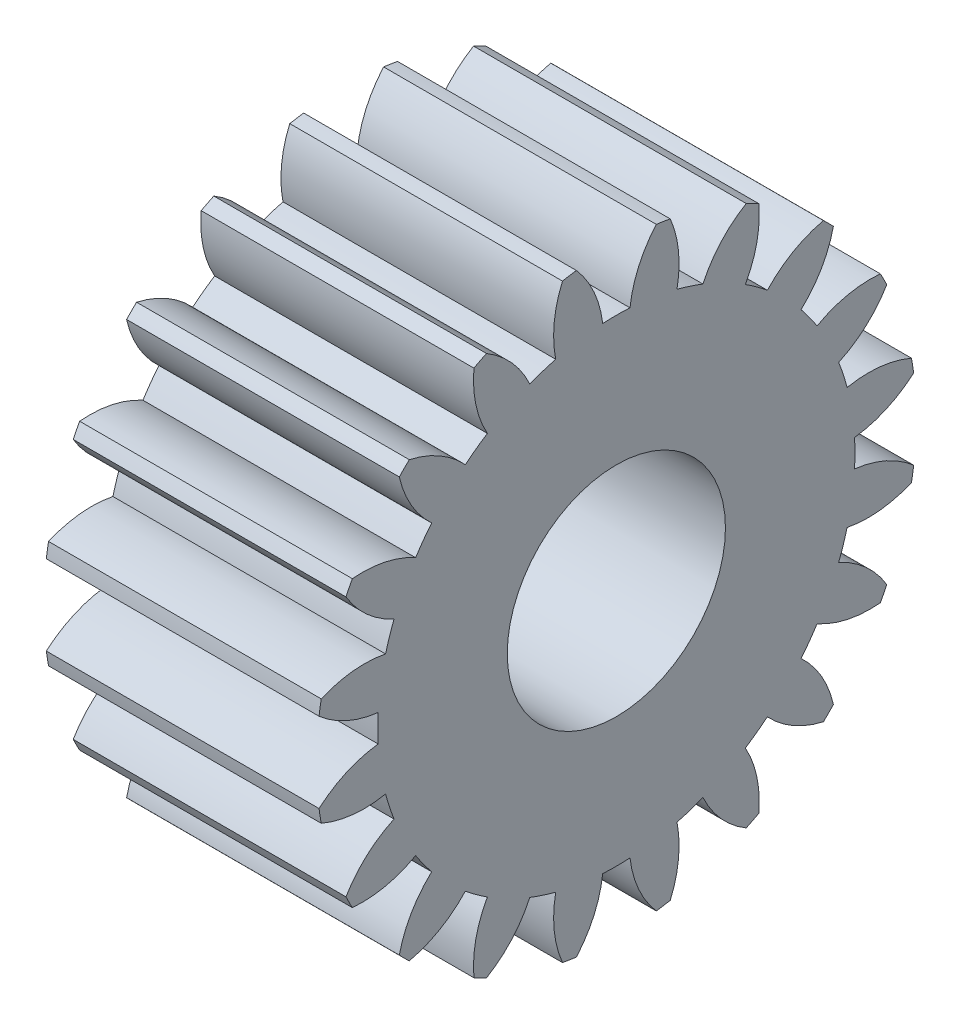
SolidWorks part; units mm, degrees
ref_plane "Plane1" through (0, 0, 0) normal (0, 0, 1) x (1, 0, 0)
ref_plane "Plane2" through (0, 0, 0) normal (0, 1, 0) x (1, 0, 0)
ref_plane "Plane3" through (0, 0, 0) normal (1, 0, 0) x (0, 0, -1)
other "Configuration Table"
sketch "HoldingSke" plane through (0, 0, 0) normal (0, 1, 0) x (1, 0, 0)
  line L0 (0, 0) -> (0.9397, -0.342)
  line L1 (-15, 0) -> (100, 0) construction
  line L2 (0, 0) -> (-2.1039, 2.3779)
  line L3 (0, 0) -> (-11.863, 4.5341)
  line L4 (0, 0) -> (8.1152, 2.9537)
  line L5 (0, 0) -> (-46.8476, -17.4728)
  line L6 (0, 0) -> (-8.2896, -5.593)
  line L7 (-2.1039, 2.3779) -> (8.6586, 51.2059)
  line L8 (-76.2, 54.61) -> (-74.8, 54.61)
  line L9 (-71.009, 38.7566) -> (-53.1078, 45.2721)
  line L10 (-76.2, 71.12) -> (104.1128, 71.12)
  line L11 (0, 0) -> (-10, 0)
  line L12 (-76.2, 101.6) -> (-76.162, 101.6)
  line L13 (24.9733, 27.94) -> (52.9518, 28.4284)
  line L14 (24.9733, 27.94) -> (24.9743, 27.94)
  line L15 (24.9733, 27.94) -> (100.4006, 29.5858)
  line L16 (-63.627, -1) -> (-12.827, -1)
  circle A0 centre (0, 0) radius 4
  circle A1 centre (0, 0) radius 8.749
  circle A2 centre (0, 0) radius 37.5
  circle A3 centre (0, 0) radius 4
  dimension "MHD" = 17.498
  dimension "Hub_dia" = 75
  dimension "Bore" = 8
  dimension "MBD" = 8
  dimension "Num_teeth" = 20
  dimension "Pitch" = 1
  dimension "Overall_len" = 50
  dimension "Show_teeth" = 20
  dimension "Thickness" = 10
  dimension "OAL" = 50.0001
  dimension "T_dim" = 1.4
  dimension "Ap" = 20
  dimension "H" = 19.05
  dimension "Pitch_radius" = 180.3128
  dimension "Width" = 10
  dimension "Backlash" = 0.038
  dimension "Addendum_fac" = 1
  dimension "Dedendum_fac" = 1.25
  dimension "Clearance_fac" = 0.25
  dimension "Dedendum_add" = 0.001
  dimension "Module" = 1
sketch "BasProSke" plane through (0, 0, 0) normal (0, 1, 0) x (1, 0, 0)
  line L0 (-10, 0) -> (60, 0) construction
  line L1 (0, 0) -> (0, 11)
  line L2 (0, 0) -> (10, 0)
  line L3 (10, 0) -> (10, 11)
  line L4 (10, 11) -> (0, 11)
  dimension "Thickness" = 10
  dimension "Diameter" = 22
revolve "Base-Revolve" add sketch "BasProSke" angle 360 about L0
sketch "TooCutSke" plane through (0, 0, 0) normal (1, 0, 0) x (0, 0, -1)
  line L1 (0, 0) -> (0, 107) construction
  line L2 (0, 0) -> (-0.8511, 9.9637) construction
  line L3 (0, 0) -> (-3.1206, 19.7028) construction
  line L4 (-0.8511, 9.9637) -> (-1.5603, 9.8514) construction
  arc A0 (0.4999, 8.7347) -> (-0.4999, 8.7347) centre (0, 0) ccw
  arc A1 (1.4852, 10.9249) -> (-1.4852, 10.9249) centre (0, 0) ccw
  circle A2 centre (0, 0) radius 10 construction
  circle A3 centre (0, 0) radius 9.3969 construction
  arc A4 (-0.4999, 8.7347) -> (-1.4852, 10.9249) centre (-4.4722, 8.2645) ccw
  arc A5 (1.4852, 10.9249) -> (0.4999, 8.7347) centre (4.4722, 8.2645) ccw
  dimension "Root_dia" = 17.498
  dimension "Overcut_dia" = 22.0508
  dimension "Pitch_dia" = 20
  dimension "Base_dia" = 18.7939
  dimension "Flank_rad" = 4
  dimension "Half_ang" = 9
  dimension "Half_CT" = 0.7181
extrude "ToothCut" cut sketch "TooCutSke" along normal through all
fillet "Breaks" [suppressed] radius 0.02
fillet "RootFillets" [suppressed] radius 0.251
pattern_circular "TeethCuts" count 20 every 18 about axis through (-10, 0, 0) along (1, 0, 0) of "ToothCut", "RootFillets", "Breaks"
sketch "HubNeaOneSke" plane through (0, 0, 0) normal (-1, 0, 0) x (0, 0, 1)
  circle A0 centre (0, 0) radius 8.749
  dimension "Diameter" = 17.498
extrude "HubNearOne" [suppressed] add sketch "HubNeaOneSke" along normal blind 40.0001
sketch "HubNeaBotSke" plane through (0, 0, 0) normal (-1, 0, 0) x (0, 0, 1)
  circle A0 centre (0, 0) radius 8.749
  dimension "Diameter" = 17.498
extrude "HubNearBoth" [suppressed] add sketch "HubNeaBotSke" along normal blind 20
ref_plane "FarPln" through (10, 0, 0) normal (1, 0, 0) x (0, 0, -1)
sketch "HubFarSke" plane through (10, 0, 0) normal (1, 0, 0) x (0, 0, -1)
  circle A0 centre (0, 0) radius 8.749
  dimension "Diameter" = 17.498
extrude "HubFar" [suppressed] add sketch "HubFarSke" along normal blind 20
sketch "BorSke" plane through (0, 0, 0) normal (1, 0, 0) x (0, 0, -1)
  circle A0 centre (0, 0) radius 4
  dimension "Diameter" = 8
extrude "Bore" cut sketch "BorSke" along normal mid plane 100.0001
sketch "KeySke" plane through (0, 0, 0) normal (1, 0, 0) x (0, 0, -1)
  line L0 (-1.5, 0) -> (-1.5, 5.4)
  line L1 (-1.5, 5.4) -> (1.5, 5.4)
  line L2 (1.5, 5.4) -> (1.5, 0)
  line L3 (0, 0) -> (0, 34) construction
  line L4 (-1.5, 0) -> (1.5, 0)
  dimension "Offset" = 5.4
  dimension "Width" = 3
extrude "Keyway" [suppressed] cut sketch "KeySke" along normal mid plane 100.0001
pattern_circular "Keyway2" [suppressed] count 2 every 90 about axis through (-10, 0, 0) along (1, 0, 0)
equation "' \"Module@HoldingSke\" = 6.35"
equation "' \"Num_teeth@HoldingSke\" = 12"
equation "' \"Ap@HoldingSke\" =  20"
equation "' \"Ap@HoldingSke\" = 20"
equation "' \"Width@HoldingSke\" = 0.5 * 25.4"
equation "' \"Hub_dia@HoldingSke\"= 1 * 25.4"
equation "' \"Hub_dia@HoldingSke\" = 1 * 25.4"
equation "' \"Overall_len@HoldingSke\" = 1.0 * 25.4"
equation "' \"Bore@HoldingSke\" = 0.75 * 25.4"
equation "' \"T_dim@HoldingSke\" = 0.1 * 25.4"
equation "' \"Width@KeySke\" = 0.25 * 25.4"
equation "' \"Show_teeth@HoldingSke\" = 13"
equation "' \"Backlash@HoldingSke\" = 0.009 * 25.4"
equation "' \"Addendum_fac@HoldingSke\" = 1.0"
equation "' \"Dedendum_fac@HoldingSke\" = 1.25"
equation "' \"Dedendum_add@HoldingSke\" = 0.00005 * 25.4"
equation "' \"Clearance_fac@HoldingSke\" = 0.25"
equation "\"Pitch@HoldingSke\" = 1 / \"Module@HoldingSke\""
equation "\"Overcut_dia@TooCutSke\" = (\"Num_teeth@HoldingSke\" + 2 * \"Addendum_fac@HoldingSke\") / \"Pitch@HoldingSke\" + 0.002 * 25.4"
equation "\"Pitch_dia@TooCutSke\" = \"Num_teeth@HoldingSke\" / \"Pitch@HoldingSke\""
equation "\"Base_dia@TooCutSke\" = \"Num_teeth@HoldingSke\" / \"Pitch@HoldingSke\" * cos((\"Ap@HoldingSke\"  * 3.14159265 / 180))"
equation "\"Root_dia@TooCutSke\" = (\"Num_teeth@HoldingSke\" + 2) / \"Pitch@HoldingSke\" - 2 * (\"Addendum_fac@HoldingSke\" + \"Dedendum_fac@HoldingSke\") / \"Pitch@HoldingSke\" - \"Dedendum_add@HoldingSke\" * 2"
equation "\"Half_ang@TooCutSke\" = 180 / \"Num_teeth@HoldingSke\""
equation "\"Half_CT@TooCutSke\" = \"Num_teeth@HoldingSke\" / \"Pitch@HoldingSke\" * sin((3.14159265 / 2 / \"Num_teeth@HoldingSke\")) / 2 - 7 * \"Backlash@HoldingSke\" / 4"
equation "\"Flank_rad@TooCutSke\" = \"Num_teeth@HoldingSke\" / \"Pitch@HoldingSke\" / 5"
equation "\"Radius@RootFillets\" = \"Clearance_fac@HoldingSke\" / \"Pitch@HoldingSke\" + \"Dedendum_add@HoldingSke\""
equation "\"Break_rad@Breaks\" = 0.02 / \"Pitch@HoldingSke\""
equation "\"Thickness@HoldingSke\" = \"Width@HoldingSke\""
equation "\"OAL@HoldingSke\" = \"Thickness@HoldingSke\""
equation "\"MHD@HoldingSke\" = (\"Num_teeth@HoldingSke\" + 2) / \"Pitch@HoldingSke\" - 2 * (\"Addendum_fac@HoldingSke\" + \"Dedendum_fac@HoldingSke\")  / \"Pitch@HoldingSke\" - \"Dedendum_add@HoldingSke\" * 2"
equation "\"MBD@HoldingSke\" = (\"Num_teeth@HoldingSke\" + 2) / \"Pitch@HoldingSke\" - 2 * (\"Addendum_fac@HoldingSke\" + \"Dedendum_fac@HoldingSke\")  / \"Pitch@HoldingSke\" - \"Dedendum_add@HoldingSke\" * 2 - 0.002 * 25.4"
equation "\"MHD@HoldingSke\" = ((sgn( \"MHD@HoldingSke\" - \"Hub_dia@HoldingSke\" )-1)*( \"MHD@HoldingSke\" - \"Hub_dia@HoldingSke\" ))/-2+ \"Hub_dia@HoldingSke\""
equation "\"MBD@HoldingSke\" = ((sgn( \"MBD@HoldingSke\" - \"Bore@HoldingSke\" )-1)*( \"MBD@HoldingSke\" - \"Bore@HoldingSke\" ))/-2+ \"Bore@HoldingSke\""
equation "\"OAL@HoldingSke\" = ((sgn( \"OAL@HoldingSke\" - \"Overall_len@HoldingSke\" )+1)*( \"OAL@HoldingSke\" - \"Overall_len@HoldingSke\" ))/2 + \"Overall_len@HoldingSke\" + 0.000002 * 25.4"
equation "\"Num_teeth@TeethCuts\" = int( \"Show_teeth@HoldingSke\" ) + 1"
equation "\"Num_teeth@TeethCuts\" = ((sgn( \"Num_teeth@TeethCuts\" - \"Num_teeth@HoldingSke\" )-1)*( \"Num_teeth@TeethCuts\" - \"Num_teeth@HoldingSke\" ))/-2+ \"Num_teeth@HoldingSke\""
equation "\"Num_teeth@TeethCuts\" = ((sgn( \"Num_teeth@TeethCuts\" - 2.0)+1)*( \"Num_teeth@TeethCuts\" - 2.0))/2 +2.0"
equation "\"Angle@TeethCuts\" = 360.0 / \"Num_teeth@HoldingSke\""
equation "\"Diameter@BasProSke\" = (\"Num_teeth@HoldingSke\" + 2 * \"Addendum_fac@HoldingSke\") / \"Pitch@HoldingSke\""
equation "\"Thickness@BasProSke\"  = \"Thickness@HoldingSke\""
equation "' \"Fillet_rad@BasProSke\" =  \"Thickness@HoldingSke\" * 0.05"
equation "' \"Fillet_rad@BasProSke\" = \"Thickness@HoldingSke\" * 0.05"
equation "\"MHD@HoldingSke\" = ((sgn( \"MHD@HoldingSke\" - \"Root_dia@TooCutSke\" )-1)*( \"MHD@HoldingSke\" - \"Root_dia@TooCutSke\" ))/-2+ \"Root_dia@TooCutSke\""
equation "\"Diameter@HubNeaOneSke\" = \"MHD@HoldingSke\""
equation "\"Length@HubNearOne\" = \"OAL@HoldingSke\" - \"Thickness@BasProSke\""
equation "\"Diameter@HubNeaBotSke\" = \"MHD@HoldingSke\""
equation "\"Length@HubNearBoth\" = ( \"OAL@HoldingSke\" - \"Thickness@BasProSke\" ) / 2.0"
equation "\"Thickness@FarPln\" = \"Thickness@BasProSke\""
equation "\"Diameter@HubFarSke\" = \"MHD@HoldingSke\""
equation "\"Length@HubFar\" = ( \"OAL@HoldingSke\" - \"Thickness@BasProSke\" ) / 2.0"
equation "\"Diameter@BorSke\" = \"MBD@HoldingSke\""
equation "\"D1@Bore\" = \"OAL@HoldingSke\" * 2.0"
equation "\"D1@Keyway\" = \"OAL@HoldingSke\" * 2.0"
equation "\"Offset@KeySke\" = \"T_dim@HoldingSke\" + \"MBD@HoldingSke\" / 2.0"
